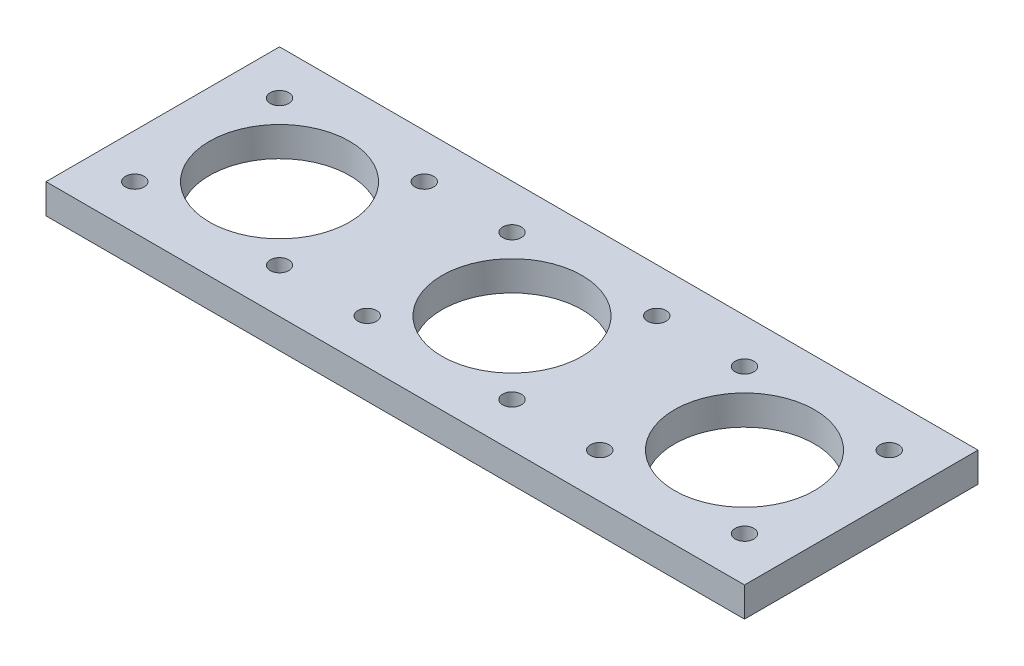
SolidWorks part; units mm, degrees
ref_plane "Front Plane" through (0, 0, 0) normal (0, 0, 1) x (1, 0, 0)
ref_plane "Top Plane" through (0, 0, 0) normal (0, 1, 0) x (1, 0, 0)
ref_plane "Right Plane" through (0, 0, 0) normal (1, 0, 0) x (0, 0, -1)
sketch "Sketch1" plane through (0, 0, 0) normal (0, 1, 0) x (1, 0, 0)
  line L1 (-25, -25) -> (25, -25)
  line L2 (-25, -25) -> (-25, 25)
  line L3 (-25, 25) -> (25, 25)
  line L4 (25, -25) -> (25, 25)
  line L5 (-25, -25) -> (25, 25) construction
  line L6 (-25, 25) -> (25, -25) construction
  point P0 (0, 0)
  dimension "D1" = 50
extrude "Boss-Extrude1" add sketch "Sketch1" along normal blind 6.35
sketch "Sketch2" plane through (0, 6.35, 0) normal (0, 1, 0) x (1, 0, 0)
  circle A0 centre (0, 0) radius 15
  dimension "D1" = 30
extrude "Cut-Extrude1" cut sketch "Sketch2" against normal through all and the other way through all
sketch "Sketch3" plane through (0, 6.35, 0) normal (0, 1, 0) x (1, 0, 0)
  line L0 (0, 0) -> (-15.5, 0) construction
  line L1 (-15.5, 0) -> (-15.5, 15.5) construction
  circle A0 centre (-15.5, 15.5) radius 2
  dimension "D1" = 4
  dimension "D2" = 15.5
extrude "Cut-Extrude2" cut sketch "Sketch3" against normal through all
mirror "Mirror1" about plane through (0, 0, 0) normal (1, 0, 0) of "Cut-Extrude2"
mirror "Mirror2" about plane through (0, 0, 0) normal (0, 0, 1) of "Mirror1", "Cut-Extrude2"
pattern_linear "LPattern2" count 3 spacing 49.784 along (1, 0, 0) of bodies 105
combine bodies "Combine1" operation type add bodies to combine 105 108 109
